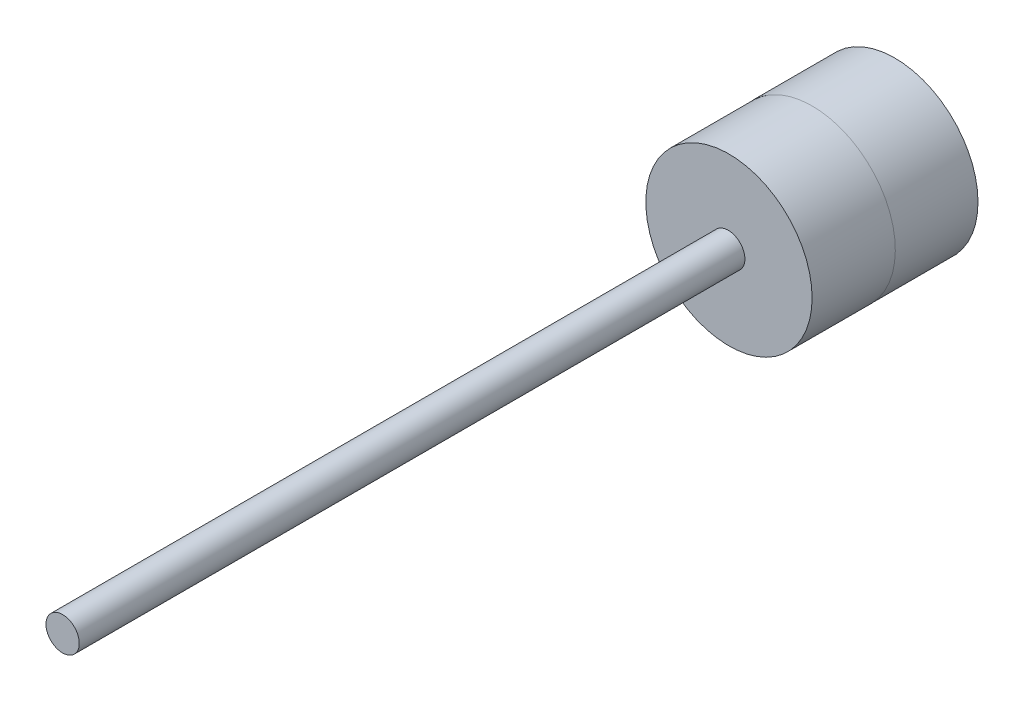
SolidWorks part; units mm, degrees
ref_plane "Front Plane" through (0, 0, 0) normal (0, 0, 1) x (1, 0, 0)
ref_plane "Top Plane" through (0, 0, 0) normal (0, 1, 0) x (1, 0, 0)
ref_plane "Right Plane" through (0, 0, 0) normal (1, 0, 0) x (0, 0, -1)
sketch "Sketch8" plane through (0, 0, 0) normal (0, 0, 1) x (1, 0, 0)
  line L0 (-48.4521, 26.2927) -> (-46.4549, 26.2927) construction
  line L1 (-46.4549, 26.2927) -> (-46.4549, 27.7965)
  line L2 (-46.4549, 26.2927) -> (-46.4549, 24.789)
  arc A0 (-46.4549, 27.7965) -> (-46.4549, 24.789) centre (-48.4521, 26.2927) ccw
  circle A1 centre (-48.4521, 26.2927) radius 5
extrude "Boss-Extrude3" add sketch "Sketch8" along normal blind 5
sketch "Sketch9" plane through (0, 0, 5) normal (0, 0, 1) x (1, 0, 0)
  circle A0 centre (-48.4164, 26.3175) radius 4.9963
extrude "Boss-Extrude4" add sketch "Sketch9" along normal blind 5
sketch "Sketch10" plane through (0, 0, 10) normal (0, 0, 1) x (1, 0, 0)
  circle A0 centre (-48.4602, 26.3218) radius 1
extrude "Boss-Extrude5" add sketch "Sketch10" along normal blind 40
